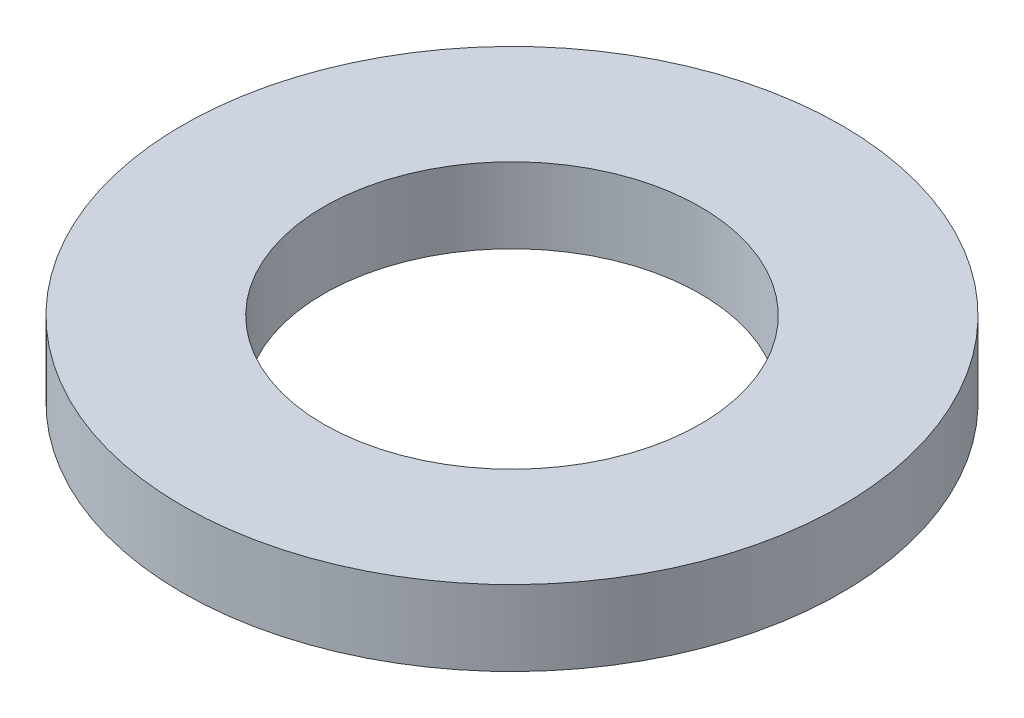
SolidWorks part; units mm, degrees
ref_plane "Front Plane" through (0, 0, 0) normal (0, 0, 1) x (1, 0, 0)
ref_plane "Top Plane" through (0, 0, 0) normal (0, 1, 0) x (1, 0, 0)
ref_plane "Right Plane" through (0, 0, 0) normal (1, 0, 0) x (0, 0, -1)
sketch "Sketch1" plane through (0, 0, 0) normal (0, 1, 0) x (1, 0, 0)
  circle A0 centre (0, 0) radius 7
  circle A1 centre (0, 0) radius 4
  dimension "D1" = 14
  dimension "D2" = 8
extrude "Boss-Extrude1" add sketch "Sketch1" along normal blind 1.6
